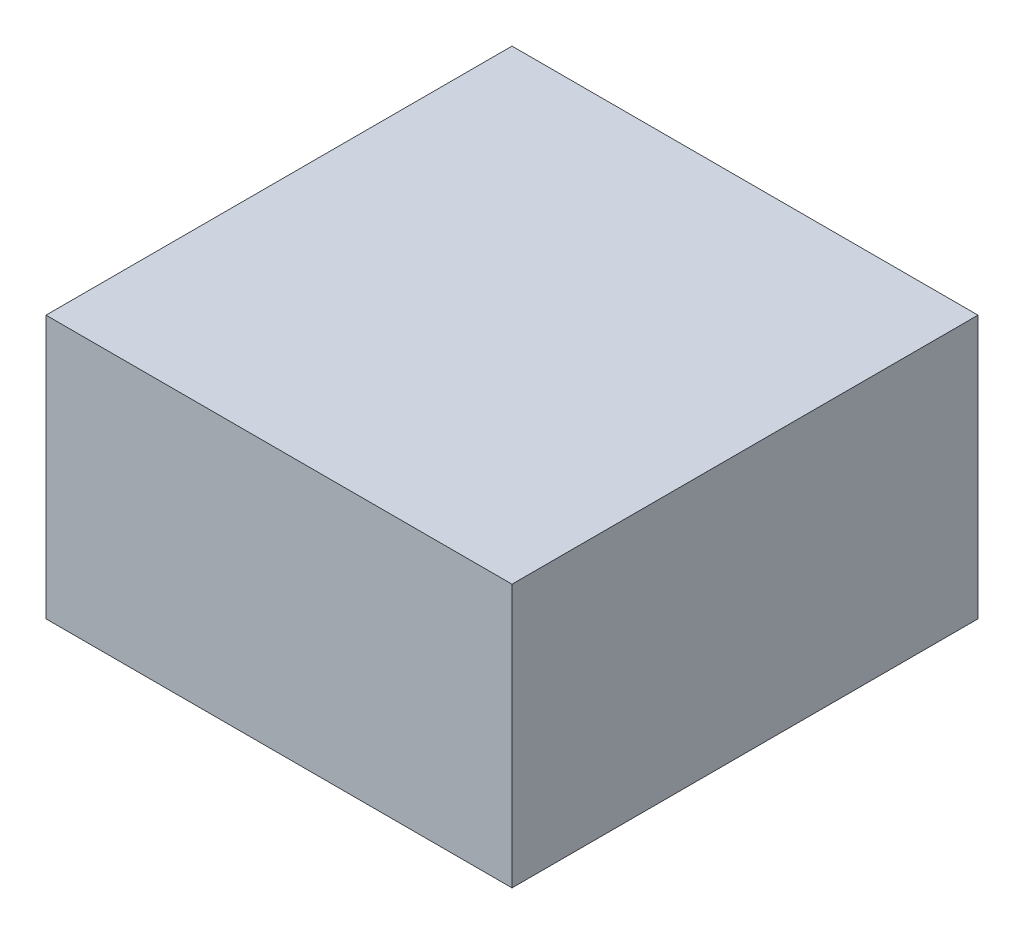
SolidWorks part; units mm, degrees
material "1060 Alloy"
ref_plane "Front Plane" through (0, 0, 0) normal (0, 0, 1) x (1, 0, 0)
ref_plane "Top Plane" through (0, 0, 0) normal (0, 1, 0) x (1, 0, 0)
ref_plane "Right Plane" through (0, 0, 0) normal (1, 0, 0) x (0, 0, -1)
sketch "Sketch1" plane through (0, 0, 0) normal (0, 1, 0) x (1, 0, 0)
  line L0 (-22.5, 22.5) -> (22.5, -22.5) construction
  line L1 (-22.5, 22.5) -> (22.5, 22.5)
  line L2 (-22.5, 22.5) -> (-22.5, -22.5)
  line L3 (-22.5, -22.5) -> (22.5, -22.5)
  line L4 (22.5, 22.5) -> (22.5, -22.5)
  dimension "D1" = 45
extrude "Boss-Extrude1" add sketch "Sketch1" along normal blind 25.4
